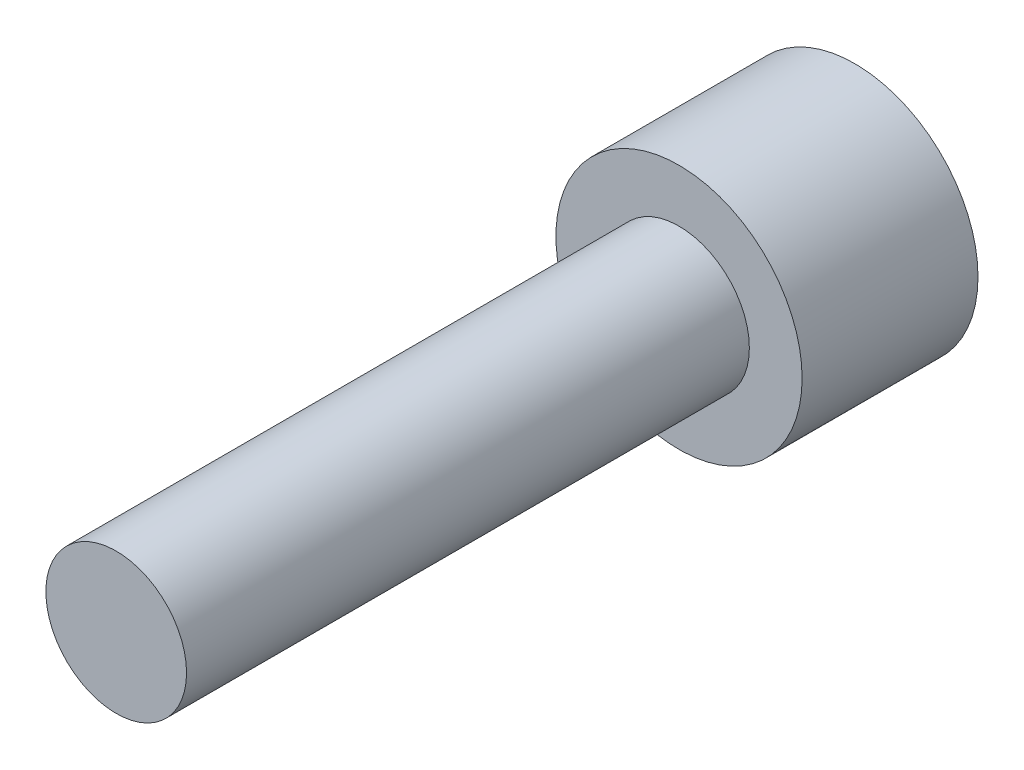
SolidWorks part; units mm, degrees
ref_plane "Alzado" through (0, 0, 0) normal (0, 0, 1) x (1, 0, 0)
ref_plane "Planta" through (0, 0, 0) normal (0, 1, 0) x (1, 0, 0)
ref_plane "Vista lateral" through (0, 0, 0) normal (1, 0, 0) x (0, 0, -1)
sketch "Croquis1" plane through (0, 0, 0) normal (0, 0, 1) x (1, 0, 0)
  circle A0 centre (0, 0) radius 1.75
  dimension "D1" = 3.5
extrude "Saliente-Extruir1" add sketch "Croquis1" along normal blind 2.5
ref_plane "Plano1" through (0, 0, 2.5) normal (0, 0, 1) x (1, 0, 0)
sketch "Croquis2" plane through (0, 0, 2.5) normal (0, 0, 1) x (1, 0, 0)
  circle A0 centre (0, 0) radius 1
  dimension "D1" = 2
extrude "Saliente-Extruir2" add sketch "Croquis2" along normal blind 8
ref_plane "Plano2" through (0, 0, 0) normal (0, 0, -1) x (-1, 0, 0)
sketch "Croquis3" plane through (0, 0, 0) normal (0, 0, -1) x (-1, 0, 0)
  line L1 (1.4434, 0) -> (0.7217, 1.25)
  line L2 (0.7217, 1.25) -> (-0.7217, 1.25)
  line L3 (-0.7217, 1.25) -> (-1.4434, 0)
  line L4 (-1.4434, 0) -> (-0.7217, -1.25)
  line L5 (-0.7217, -1.25) -> (0.7217, -1.25)
  line L6 (0.7217, -1.25) -> (1.4434, 0)
  circle A0 centre (0, 0) radius 1.25 construction
  dimension "D1" = 2.5
extrude "Cortar-Extruir1" cut sketch "Croquis3" against normal blind 1.75
